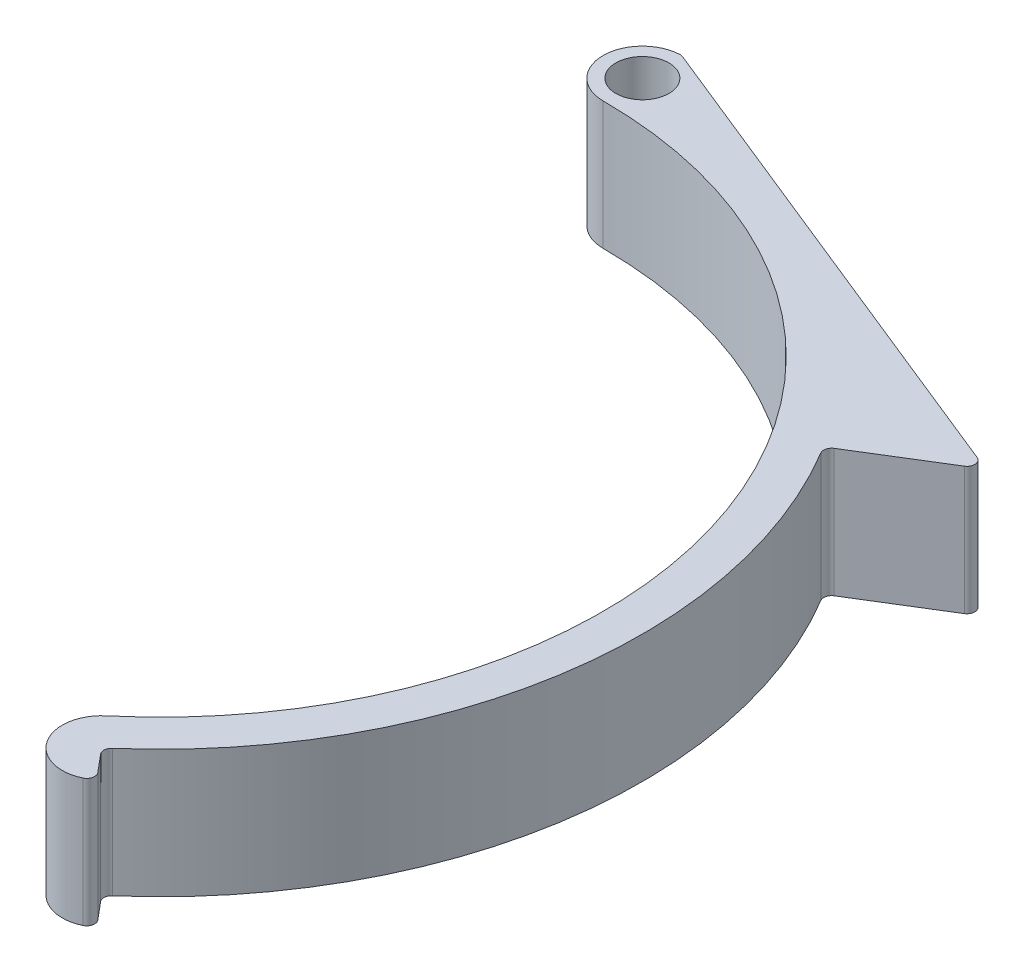
SolidWorks part; units mm, degrees
ref_plane "Front Plane" through (0, 0, 0) normal (0, 0, 1) x (1, 0, 0)
ref_plane "Top Plane" through (0, 0, 0) normal (0, 1, 0) x (1, 0, 0)
ref_plane "Right Plane" through (0, 0, 0) normal (1, 0, 0) x (0, 0, -1)
sketch "Sketch1" plane through (0, 0, 0) normal (0, 1, 0) x (1, 0, 0)
  line L0 (0, 0) -> (28.9254, -34.472) construction
  line L1 (0, 0) -> (0, -45) construction
  line L2 (0, 0) -> (53.3468, -63.5762) construction
  line L3 (0, 53) -> (51.921, 32.0189)
  line L4 (51.921, 32.0189) -> (41.707, 25.7201)
  line L5 (0, 53) -> (0, 49)
  line L6 (31.4966, -37.5362) -> (34.0677, -40.6004)
  line L7 (0, 49) -> (0, 53)
  circle A0 centre (0, 0) radius 45 construction
  arc A1 (0, 45) -> (28.9254, -34.472) centre (0, 0) cw
  arc A2 (0, 45) -> (0, 53) centre (0, 49) cw
  arc A3 (28.9254, -34.472) -> (34.0677, -40.6004) centre (31.4966, -37.5362) ccw
  arc A4 (31.4966, -37.5362) -> (0, 49) centre (0, 0) ccw
  circle A5 centre (0, 49) radius 2.7
  arc A6 (41.707, 25.7201) -> (0, 49) centre (0, 0) ccw
  point P10 (0, 0)
  dimension "D1" = 90
  dimension "D5" = 56
  dimension "D6" = 5.4
  dimension "D2" = 40
  dimension "D3" = 8
  dimension "D4" = 4
  dimension "D7" = 12
extrude "Boss-Extrude1" add sketch "Sketch1" along normal blind 13 contours A5 L5 A2 A1 A3 L6 A4 | A5 A4 L4 L3 L5
fillet "Fillet1" radius 0.8 5 edges at (0, 6.5, -53) (31.4966, 6.5, 37.5362) (34.0677, 6.5, 40.6004) (51.921, 6.5, -32.0189) (41.707, 6.5, -25.7201)
